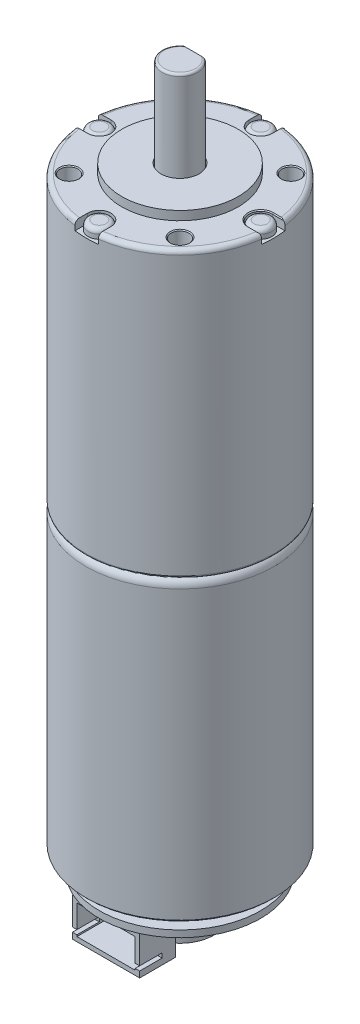
SolidWorks part; units mm, degrees
ref_plane "Front Plane" through (0, 0, 0) normal (0, 0, 1) x (1, 0, 0)
ref_plane "Top Plane" through (0, 0, 0) normal (0, 1, 0) x (1, 0, 0)
ref_plane "Right Plane" through (0, 0, 0) normal (1, 0, 0) x (0, 0, -1)
sketch "草圖1" plane through (0, 0, 0) normal (0, 1, 0) x (1, 0, 0)
  circle A0 centre (0, 0) radius 21
  dimension "D1" = 42
extrude "填料-伸長1" add sketch "草圖1" along normal blind 66.5
fillet "圓角1" radius 2 1 edges at (0, 66.5, 21)
sketch "草圖4" plane through (0, 66.5, 0) normal (0, 1, 0) x (1, 0, 0)
  circle A0 centre (0, 0) radius 21
  dimension "D1" = 42
extrude "填料-伸長2" add sketch "草圖4" along normal blind 63.5
sketch "草圖6" plane through (0, 130, 0) normal (0, 1, 0) x (1, 0, 0)
  circle A0 centre (0, 0) radius 13
  dimension "D1" = 26
extrude "填料-伸長3" add sketch "草圖6" along normal blind 2
sketch "草圖7" plane through (0, 132, 0) normal (0, 1, 0) x (1, 0, 0)
  circle A0 centre (0, 0) radius 4
  dimension "D1" = 8
extrude "填料-伸長4" add sketch "草圖7" along normal blind 20
sketch "草圖8" plane through (0, 152, 0) normal (0, 1, 0) x (1, 0, 0)
  line L0 (-2.6458, 3) -> (2.6458, 3)
  line L1 (-23.1, 0) -> (23.1, 0) construction
  line L2 (0, 4) -> (0, 3) construction
  arc A0 (-2.6458, 3) -> (2.6458, 3) centre (0, 0) cw
  circle A1 centre (0, 0) radius 4 construction
  dimension "D1" = 1
extrude "除料-伸長3" cut sketch "草圖8" against normal blind 12
fillet "圓角2" radius 0.5 1 edges at (0, 66.5, 21)
fillet "圓角4" radius 0.5 1 edges at (0, 152, 4)
sketch "草圖9" plane through (0, 130, 0) normal (0, 1, 0) x (1, 0, 0)
  line L0 (15.4, 0) -> (0, 0) construction
  line L1 (18, 2.6) -> (18, -2.6) construction
  line L2 (18, 2.6) -> (21, 2.6)
  line L4 (18, -2.6) -> (21, -2.6)
  line L5 (21, 2.6) -> (21, -2.6)
  line L6 (15.4, 0) -> (18, 0) construction
  arc A0 (18, 2.6) -> (18, -2.6) centre (18, 0) ccw
  dimension "D1" = 5.2
  dimension "D2" = 18
  dimension "D3" = 3
  dimension "D4" = 5.2
extrude "除料-伸長4" cut sketch "草圖9" against normal blind 2 and the other way through all
chamfer "導角1" distance 0.2 angle 45 3 edges at (19.4192, 130, 2.6) (15.4, 130, 0) (19.4192, 130, -2.6)
sketch "草圖11" plane through (0, 128, 0) normal (0, 1, 0) x (1, 0, 0)
  line L0 (18, 2.6) -> (18, -2.6) construction
  circle A0 centre (18, 0) radius 2.5
  dimension "D1" = 5
extrude "填料-伸長5" add sketch "草圖11" along normal blind 2
fillet "圓角5" radius 1 1 edges at (18, 130, 2.5)
sketch "草圖10" plane through (0, 130, 0) normal (0, 1, 0) x (1, 0, 0)
  line L0 (0, 0) -> (12.3744, 12.3744) construction
  line L1 (0, 0) -> (18, 0) construction
  circle A0 centre (0, 0) radius 21 construction
  circle A1 centre (12.3744, 12.3744) radius 2
  dimension "D3" = 4
  dimension "D1" = 45
  dimension "D2" = 17.5
extrude "除料-伸長5" cut sketch "草圖10" against normal blind 5
chamfer "導角2" distance 0.2 angle 45 1 edges at (12.3744, 130, -10.3744)
pattern_circular "環狀複製排列3" count 4 over 360 about axis through (0, 0, 0) along (0, 1, 0) of "導角2", "除料-伸長5", "除料-伸長4", "填料-伸長5", "圓角5"
sketch "草圖13" plane through (0, 0, 0) normal (0, -1, 0) x (1, 0, 0)
  circle A0 centre (0, 0) radius 10
  dimension "D1" = 20
extrude "填料-伸長6" add sketch "草圖13" along normal blind 3.5
sketch "草圖14" plane through (0, -3.5, 0) normal (0, -1, 0) x (1, 0, 0)
  circle A0 centre (0, 0) radius 8.5
  dimension "D1" = 17
extrude "除料-伸長7" cut sketch "草圖14" against normal blind 3.5
sketch "草圖15" plane through (0, 0, 0) normal (0, 0, 1) x (1, 0, 0)
  line L1 (-7.5, 0) -> (7.5, 0)
  line L2 (-7.5, 0) -> (-7.5, -3.5)
  line L3 (-7.5, -3.5) -> (7.5, -3.5)
  line L4 (7.5, 0) -> (7.5, -3.5)
  point P4 (0, 0)
  dimension "D1" = 15
  dimension "D2" = 3.5
extrude "除料-伸長8" cut sketch "草圖15" against normal through all and the other way through all
sketch "草圖16" plane through (0, 0, 0) normal (0, -1, 0) x (1, 0, 0)
  circle A0 centre (0, 0) radius 18
  dimension "D1" = 36
extrude "填料-伸長7" add sketch "草圖16" along normal blind 1.5 from surface at 3.5 starting at face at (8.375, -3.5, 0)
sketch "草圖17" plane through (0, -5, 0) normal (0, -1, 0) x (1, 0, 0)
  circle A0 centre (0, 0) radius 1
  dimension "D1" = 2
extrude "填料-伸長8" add sketch "草圖17" along normal blind 2 and the other way blind 5 contours A0
sketch "草圖18" plane through (0, -7, 0) normal (0, -1, 0) x (-1, 0, 0)
  circle A0 centre (0, 0) radius 7.5
  dimension "D1" = 15
extrude "填料-伸長9" add sketch "草圖18" along normal blind 6.5
sketch "草圖19" plane through (0, 132, 0) normal (0, 1, 0) x (1, 0, 0)
  circle A0 centre (0, 0) radius 4.25
  circle A1 centre (0, 0) radius 4
  dimension "D1" = 8
  dimension "D2" = 8.5
extrude "除料-伸長9" cut sketch "草圖19" against normal blind 2
chamfer "導角4" distance 0.5 angle 45 1 edges at (0, 0, 21)
sketch "草圖20" plane through (0, -5, 0) normal (0, -1, 0) x (1, 0, 0)
  line L0 (0, 12.5) -> (0, 0) construction
  line L1 (-7.5, 16.5) -> (7.5, 16.5)
  line L2 (-7.5, 16.5) -> (-7.5, 8.5)
  line L3 (-7.5, 8.5) -> (7.5, 8.5)
  line L4 (7.5, 16.5) -> (7.5, 8.5)
  line L5 (-7.5, 16.5) -> (7.5, 8.5) construction
  line L6 (-7.5, 8.5) -> (7.5, 16.5) construction
  point P0 (0, 12.5)
  dimension "D1" = 15
  dimension "D2" = 8
  dimension "D3" = 8.5
extrude "填料-伸長10" add sketch "草圖20" along normal blind 8.5
sketch "草圖21" plane through (0, 0, 16.5) normal (0, 0, 1) x (1, 0, 0)
  line L0 (-7.5, -13.5) -> (-7.5, -5) construction
  line L1 (-6.5, -6) -> (6.5, -6)
  line L2 (-6.5, -6) -> (-6.5, -12.5)
  line L3 (-6.5, -12.5) -> (6.5, -12.5)
  line L4 (6.5, -6) -> (6.5, -12.5)
  line L5 (-6.5, -6) -> (6.5, -12.5) construction
  line L6 (-6.5, -12.5) -> (6.5, -6) construction
  line L7 (7.5, -13.5) -> (-7.5, -13.5) construction
  line L8 (7.5, -13.5) -> (7.5, -5) construction
  line L9 (-7.1937, -5) -> (7.1937, -5) construction
  point P0 (0, -9.25)
  dimension "D1" = 1
  dimension "D2" = 1
  dimension "D3" = 1
  dimension "D4" = 1
extrude "除料-伸長10" cut sketch "草圖21" against normal blind 7
sketch "草圖22" plane through (7.5, 0, 0) normal (1, 0, 0) x (0, 0, -1)
  line L0 (-16.5, -13.5) -> (-16.5, -5) construction
  line L1 (-16.5, -11.15) -> (-11.5, -11.15)
  line L2 (-16.5, -11.15) -> (-16.5, -12.15)
  line L3 (-16.5, -12.15) -> (-11.5, -12.15)
  line L4 (-11.5, -11.15) -> (-11.5, -12.15)
  line L5 (-8.5, -13.5) -> (-16.5, -13.5) construction
  dimension "D1" = 1
  dimension "D2" = 5
  dimension "D3" = 1.35
extrude "除料-伸長11" cut sketch "草圖22" against normal through all
fillet "圓角7" radius 1 4 edges at (14.7778, 130, -14.9204) (14.7778, 130, 14.9204) (-14.8492, 130, 14.8492) (-14.8492, 130, -14.8492)
